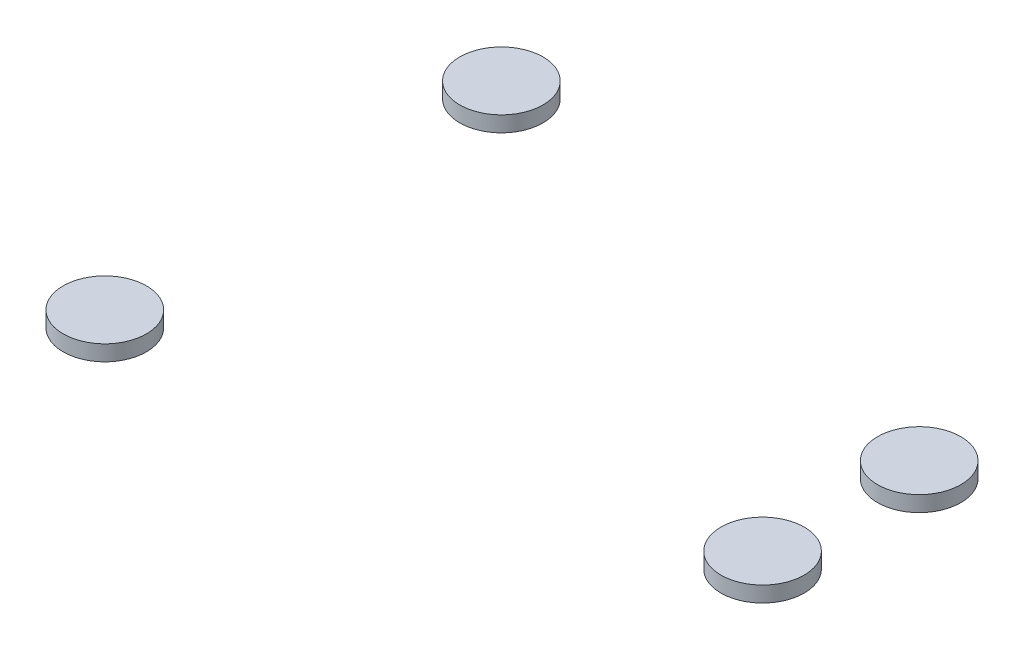
SolidWorks part; units mm, degrees
ref_plane "Front Plane" through (0, 0, 0) normal (0, 0, 1) x (1, 0, 0)
ref_plane "Top Plane" through (0, 0, 0) normal (0, 1, 0) x (1, 0, 0)
ref_plane "Right Plane" through (0, 0, 0) normal (1, 0, 0) x (0, 0, -1)
sketch "Sketch1" plane through (0, 0, 0) normal (0, 1, 0) x (1, 0, 0)
  line L0 (0, 0) -> (80.6822, 0) construction
  line L1 (-11, -19.0526) -> (0, 0) construction
  line L2 (40.6732, -7.5244) -> (20, 0) construction
  circle A0 centre (-11, -19.0526) radius 4
  circle A1 centre (40.6732, -7.5244) radius 4
  circle A2 centre (40.6732, 7.5244) radius 4
  circle A3 centre (-11, 19.0526) radius 4
  point P7 (38.9911, -7.8177)
  point P9 (-11.9002, -19.4216)
  dimension "D1" = 8
  dimension "D3" = 22
  dimension "D4" = 60
  dimension "D5" = 20
extrude "Boss-Extrude1" add sketch "Sketch1" against normal blind 1.5
